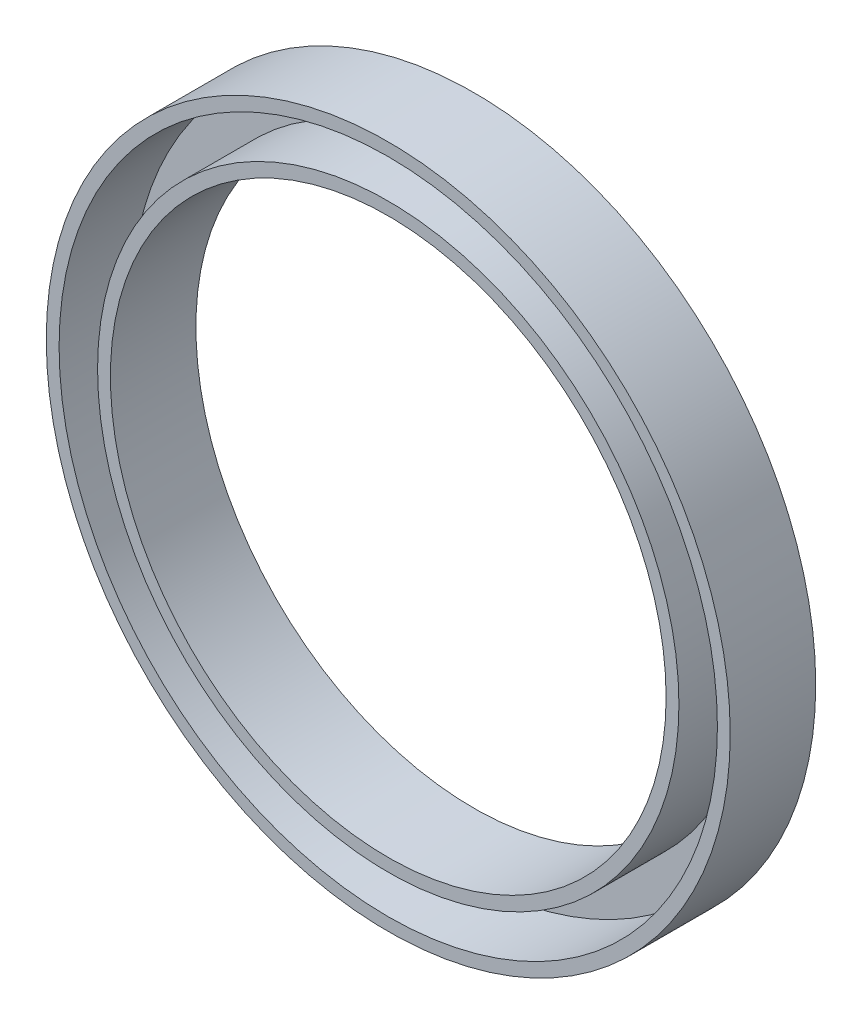
SolidWorks part; units mm, degrees
ref_plane "前视基准面" through (0, 0, 0) normal (0, 0, 1) x (1, 0, 0)
ref_plane "上视基准面" through (0, 0, 0) normal (0, 1, 0) x (1, 0, 0)
ref_plane "右视基准面" through (0, 0, 0) normal (1, 0, 0) x (0, 0, -1)
sketch "草图1" plane through (0, 0, 0) normal (0, 0, 1) x (1, 0, 0)
  circle A0 centre (0, 0) radius 32.5
  circle A1 centre (0, 0) radius 40
  dimension "D1" = 65
  dimension "D2" = 80
extrude "凸台-拉伸1" add sketch "草图1" along normal blind 10
shell "抽壳1" thickness 1.5
